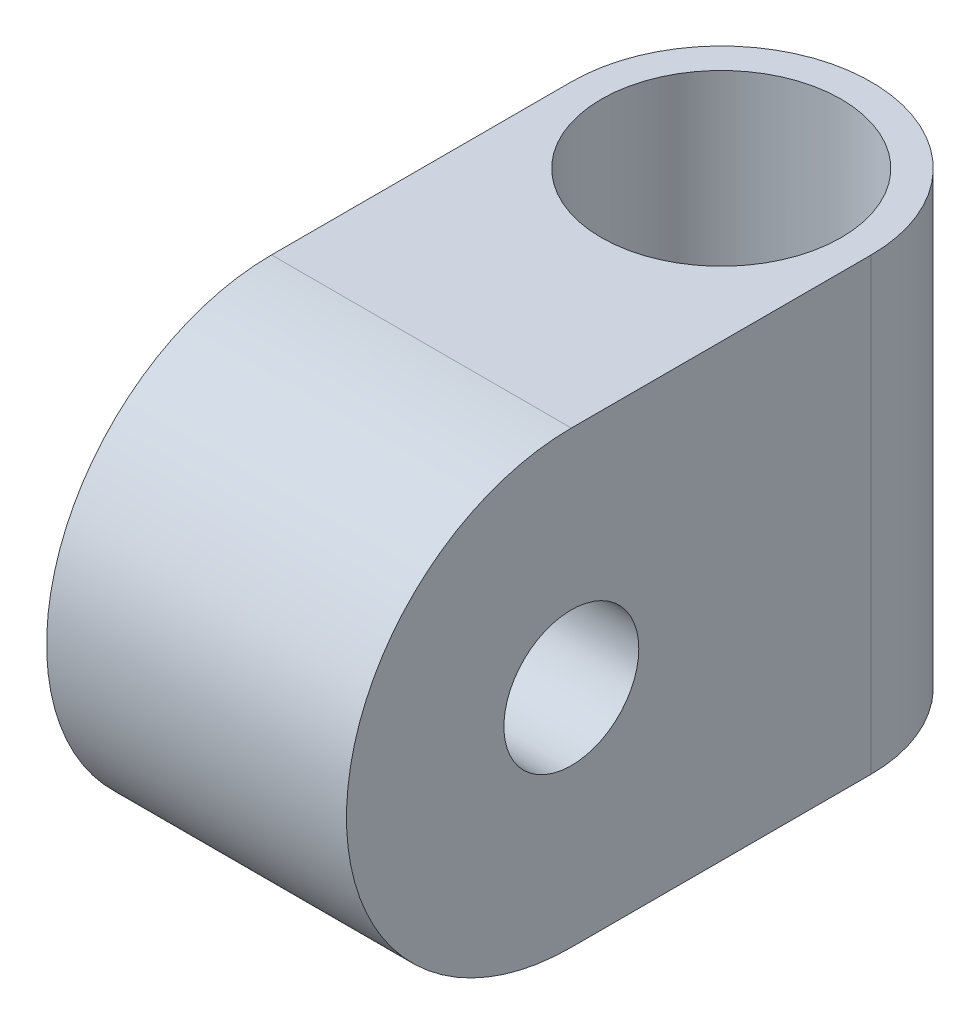
SolidWorks part; units mm, degrees
ref_plane "Front Plane" through (0, 0, 0) normal (0, 0, 1) x (1, 0, 0)
ref_plane "Top Plane" through (0, 0, 0) normal (0, 1, 0) x (1, 0, 0)
ref_plane "Right Plane" through (0, 0, 0) normal (1, 0, 0) x (0, 0, -1)
sketch "Sketch1" plane through (0, 0, 0) normal (1, 0, 0) x (0, 0, -1)
  line L1 (7.5, -7.5) -> (-7.5, -7.5)
  line L2 (7.5, -7.5) -> (7.5, 7.5)
  line L3 (7.5, 7.5) -> (-7.5, 7.5)
  line L4 (-7.5, -7.5) -> (-7.5, 7.5)
  line L5 (7.5, -7.5) -> (-7.5, 7.5) construction
  line L6 (7.5, 7.5) -> (-7.5, -7.5) construction
  arc A0 (-7.5, 7.5) -> (-7.5, -7.5) centre (-7.5, 0) ccw
  circle A1 centre (-7.5, 0) radius 2.25
  point P0 (0, 0)
  dimension "D3" = 4.5
  dimension "D1" = 15
  dimension "D2" = 15
extrude "Boss-Extrude1" add sketch "Sketch1" along normal mid plane 10 contours A1 L4 L1 L2 L3 | A1 L4 A0
sketch "Sketch2" plane through (0, 7.5, 0) normal (0, 1, 0) x (1, 0, 0)
  line L0 (5, 7.5) -> (-5, 7.5) construction
  line L1 (5, 7.5) -> (5, -7.5) construction
  line L2 (-5, 7.5) -> (-5, -7.5) construction
  line L3 (-5, 2.5) -> (-5, 10.9193)
  line L4 (-5, 10.9193) -> (5, 10.9193)
  line L5 (5, 10.9193) -> (5, 2.5)
  circle A0 centre (0, 2.5) radius 5
  circle A1 centre (0, 2.5) radius 4
  line M3 (-5, 7.5) -> (-5, -7.5)
  line M5 (5, -7.5) -> (5, 7.5)
  line M6 (5, 7.5) -> (-5, 7.5)
  dimension "D1" = 8
extrude "Cut-Extrude1" cut sketch "Sketch2" against normal through all both and the other way through all contours L5 L4 L3 M6 | A0 M6 M3 | A0 M5 M6 | A1
